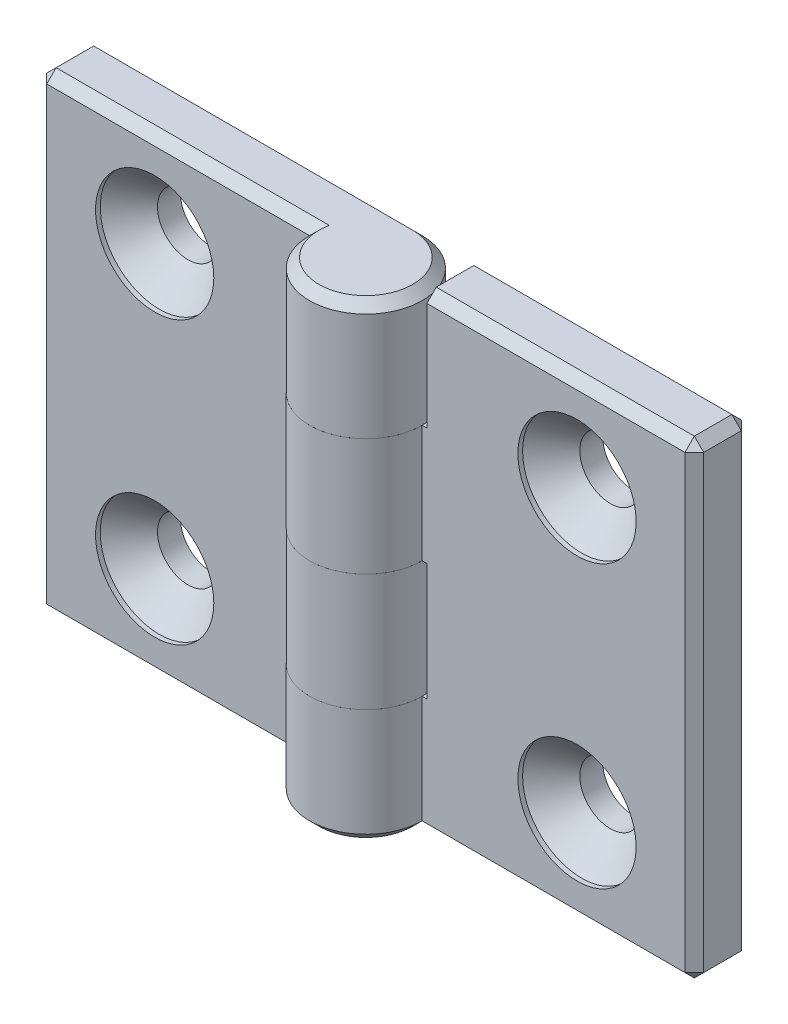
SolidWorks part; units mm, degrees
material "Нейлон"
ref_plane "Спереди" through (0, 0, 0) normal (0, 0, 1) x (1, 0, 0)
ref_plane "Сверху" through (0, 0, 0) normal (0, 1, 0) x (1, 0, 0)
ref_plane "Справа" through (0, 0, 0) normal (1, 0, 0) x (0, 0, -1)
sketch "Эскиз1" plane through (0, 0, 0) normal (0, 1, 0) x (1, 0, 0)
  line L0 (0, 6) -> (-35, 6)
  line L1 (-35, 6) -> (-35, 0)
  line L3 (-35, 0) -> (-6, 0)
  line L4 (0, 0) -> (0, 10.5526) construction
  arc A0 (-6, 0) -> (0, 6) centre (0, 0) ccw
  point P1 (0, 0)
  dimension "D1" = 70
  dimension "D2" = 6
extrude "Бобышка-Вытянуть1" add sketch "Эскиз1" along normal mid plane 50
sketch "Эскиз3" plane through (0, 0, 0) normal (0, 0, 1) x (1, 0, 0)
  line L0 (6, -25) -> (6, 25) construction
  line L1 (-6.5, 12.5) -> (6, 12.5)
  line L2 (-6.5, 12.5) -> (-6.5, 0)
  line L3 (-6.5, 0) -> (6, 0)
  line L4 (6, 12.5) -> (6, 0)
  line L5 (6, 0) -> (6, -12.5) construction
  line L6 (6, -25) -> (-6.5, -25)
  line L7 (6, -25) -> (6, -12.5)
  line L8 (6, -12.5) -> (-6.5, -12.5)
  line L9 (-6.5, -25) -> (-6.5, -12.5)
  line L10 (6, 12.5) -> (6, 25) construction
  line L11 (-6, 25) -> (-6, -25) construction
  dimension "D1" = 0.5
extrude "Вырез-Вытянуть1" cut sketch "Эскиз3" against normal through all and the other way through all
hole_wizard "Зенковка для винта с полупотайной головкой M61" positions "Эскиз4" profile "Эскиз6" countersink size "M6" standard "ISO" end condition through all
sketch "Эскиз4" plane through (0, 0, 0) normal (0, 0, 1) x (1, 0, 0)
  line L0 (-22.5, 15) -> (-22.5, -15)
  line L2 (0, 0) -> (0, 18.9001) construction
  line L3 (6, 0) -> (-6, 0) construction
  point P0 (-22.5, 15)
  point P2 (-22.5, -15)
  point P9 (-22.5, 0)
  dimension "D1" = 30
  dimension "D2" = 45
sketch "Эскиз6" plane through (-22.5, 15, 0) normal (1, 0, 0) x (0, -1, 0)
  line L0 (0, 0) -> (0, 6)
  line L1 (0, 6) -> (3.25, 6)
  line L2 (3.25, 6) -> (3.25, 3.55)
  line L3 (3.25, 3.55) -> (6.3, 0.5)
  line L4 (6.3, 0.5) -> (6.3, 0)
  line L6 (6.3, 0) -> (0, 0)
  line L7 (-3.25, 3.55) -> (-6.3, 0.5) construction
  line L11 (0, -6.35) -> (0, 107.95) construction
  dimension "Диаметр сквозного отверстия" = 6.5
  dimension "Глубина сквозного отверстия" = 6
  dimension "Диаметр зенковки" = 12.6
  dimension "Угол зенковки" = 90
  dimension "Утопленность" = 0.5
chamfer "Фаска1" distance 1 angle 45 9 edges at (-20.75, -25, 0) (-35, 0, 0) (-20.5, 25, 0) (-35, -25, -3) (-35, 25, -3) (4.2426, 25, 4.2426) (-17.5, 25, -6) (-35, 0, -6) (-20.75, -25, -6)
sketch "Угол раскрытия" plane through (0, 0, 0) normal (0, 1, 0) x (1, 0, 0)
  line L0 (0, 0) -> (0, -10)
  line L7 (0, 6) -> (-35, 6) construction
  dimension "D1" = 10
  dimension "D2" = 90
pattern_circular "Круговой массив1" count 2 over 360 about axis through (0, 0, 0) along (0, 0, 1) of bodies 106
